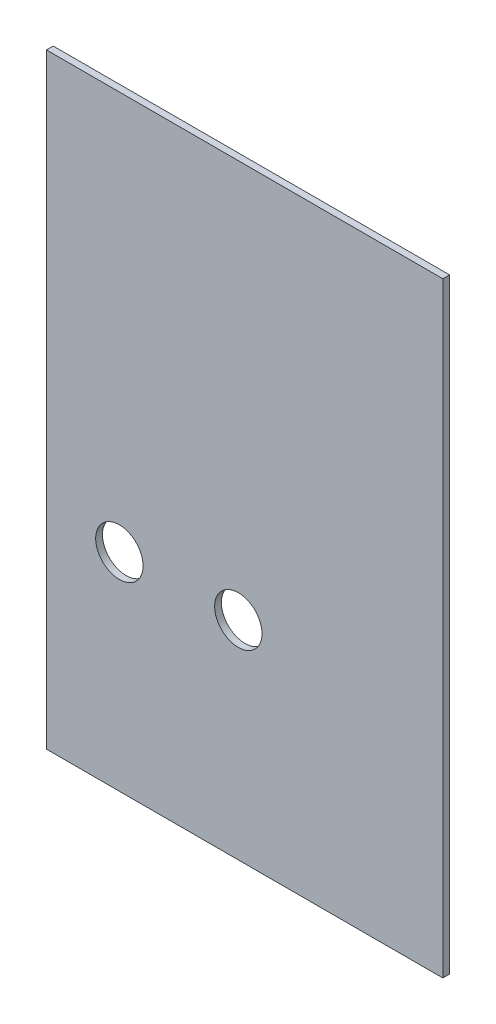
SolidWorks part; units mm, degrees
ref_plane "Front Plane" through (0, 0, 0) normal (0, 0, 1) x (1, 0, 0)
ref_plane "Top Plane" through (0, 0, 0) normal (0, 1, 0) x (1, 0, 0)
ref_plane "Right Plane" through (0, 0, 0) normal (1, 0, 0) x (0, 0, -1)
sketch "Sketch1" plane through (0, 0, 0) normal (0, 0, 1) x (1, 0, 0)
  line L0 (0, 285.1102) -> (0, 0)
  line L1 (0, 0) -> (186.617, 0)
  line L2 (186.617, 0) -> (186.617, 285.1102)
  line L6 (62.3183, 145.1102) -> (68.3183, 145.1102) construction
  line L7 (0, 285.1102) -> (186.617, 285.1102)
  line L8 (456.213, 50) -> (473.4243, 50) construction
  circle A0 centre (34.3399, 97.494) radius 11.15
  circle A1 centre (90.339, 97.8174) radius 11.15
  point P8 (0, 0)
  dimension "D2" = 22.3
  dimension "D4" = 22.3
  dimension "D1" = 50
  dimension "D3" = 140
  dimension "D5" = 34.3399
  dimension "D6" = 97.494
  dimension "D7" = 55.9991
  dimension "D8" = 96.2779
  dimension "D9" = 97.8174
  dimension "D10" = 186.617
  dimension "D11" = 285.1102
  dimension "D12" = 97.494
  dimension "D13" = 97.8174
extrude "Boss-Extrude1" add sketch "Sketch1" along normal mid plane 3.175 contours L1 L2 L7 L0
sketch "Sketch2" plane through (0, 0, 1.5875) normal (0, 0, 1) x (1, 0, 0)
  circle A0 centre (90.339, 97.8174) radius 11.15 construction
  circle A1 centre (34.3399, 97.494) radius 11.15 construction
  circle A2 centre (90.339, 97.8174) radius 11.15
  circle A3 centre (34.3399, 97.494) radius 11.15
extrude "Cut-Extrude1" cut sketch "Sketch2" against normal through all
